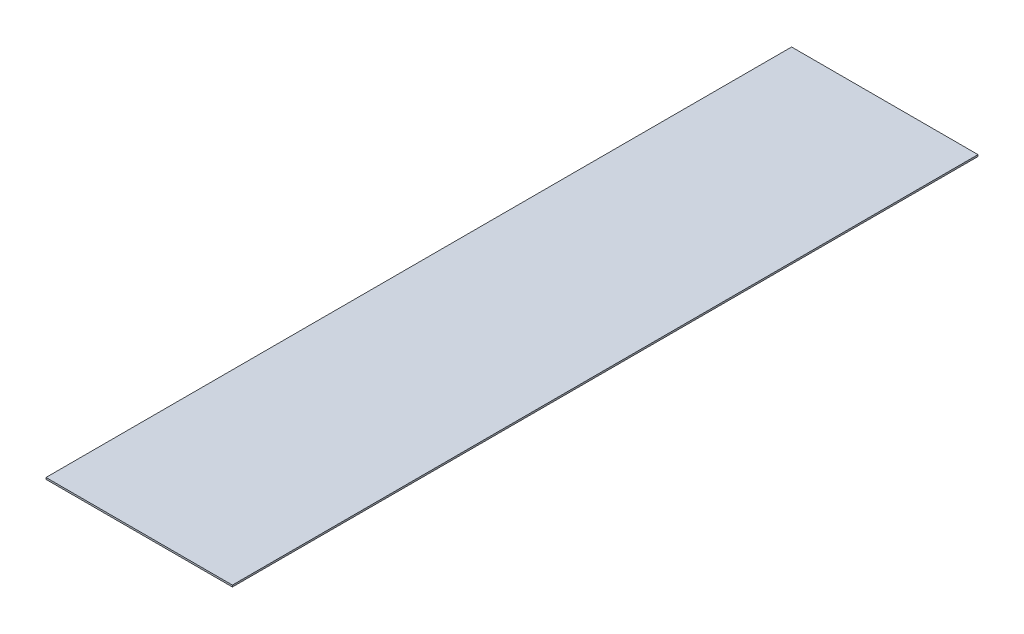
SolidWorks part; units mm, degrees
material "Teak"
ref_plane "Front Plane" through (0, 0, 0) normal (0, 0, 1) x (1, 0, 0)
ref_plane "Top Plane" through (0, 0, 0) normal (0, 1, 0) x (1, 0, 0)
ref_plane "Right Plane" through (0, 0, 0) normal (1, 0, 0) x (0, 0, -1)
sketch "Sketch1" plane through (0, 0, 0) normal (0, 1, 0) x (1, 0, 0)
  line L1 (-304.8, -1219.2) -> (304.8, -1219.2)
  line L2 (-304.8, -1219.2) -> (-304.8, 1219.2)
  line L3 (-304.8, 1219.2) -> (304.8, 1219.2)
  line L4 (304.8, -1219.2) -> (304.8, 1219.2)
  line L5 (-304.8, -1219.2) -> (304.8, 1219.2) construction
  line L6 (-304.8, 1219.2) -> (304.8, -1219.2) construction
  point P0 (0, 0)
  dimension "D1" = 609.6
  dimension "D2" = 2438.4
extrude "Boss-Extrude1" add sketch "Sketch1" along normal blind 5.5562
